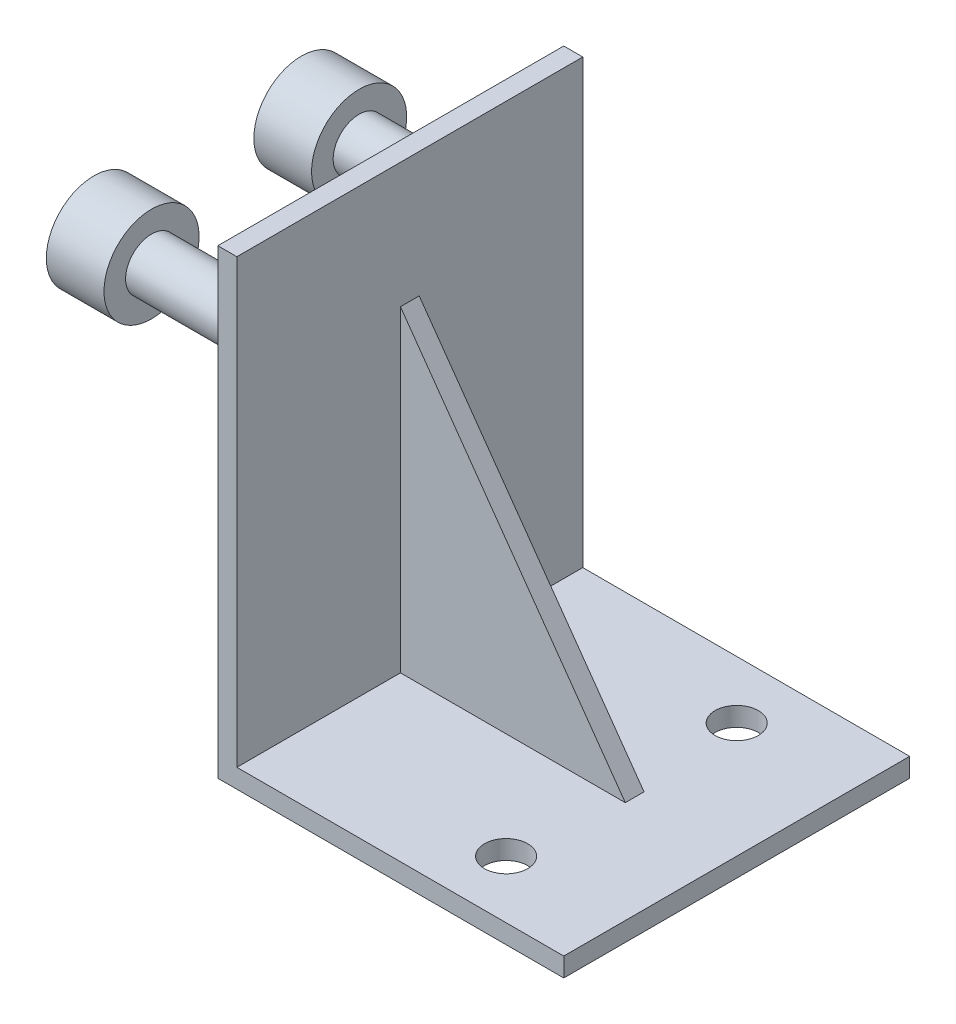
SolidWorks part; units mm, degrees
ref_plane "Front Plane" through (0, 0, 0) normal (0, 0, 1) x (1, 0, 0)
ref_plane "Top Plane" through (0, 0, 0) normal (0, 1, 0) x (1, 0, 0)
ref_plane "Right Plane" through (0, 0, 0) normal (1, 0, 0) x (0, 0, -1)
sketch "Sketch1" plane through (0, 0, 0) normal (0, 0, 1) x (1, 0, 0)
  line L0 (0, 0) -> (30.48, 0)
  line L1 (0, 40.64) -> (1.6764, 40.64)
  line L2 (0, 40.64) -> (0, 0)
  line L4 (1.6764, 40.64) -> (1.6764, 1.6764)
  line L7 (1.6764, 1.6764) -> (30.48, 1.6764)
  line L8 (30.48, 0) -> (30.48, 1.6764)
  dimension "D1" = 1.6764
  dimension "D2" = 30.48
  dimension "D3" = 40.64
extrude "Boss-Extrude1" add sketch "Sketch1" along normal mid plane 30.48 contours L4 L7 L8 L0 L2 L1
sketch "Sketch2" plane through (0, 0, 0) normal (0, 0, 1) x (1, 0, 0)
  line L0 (1.6764, 29.6164) -> (21.4884, 1.6764)
  line L1 (1.6764, 40.64) -> (1.6764, 1.6764) construction
  line L2 (1.6764, 1.6764) -> (30.48, 1.6764) construction
  line L3 (21.4884, 1.6764) -> (1.6764, 1.6764)
  line L4 (1.6764, 1.6764) -> (1.6764, 29.6164)
  dimension "D1" = 27.94
  dimension "D2" = 19.812
extrude "Boss-Extrude2" add sketch "Sketch2" along normal mid plane 1.651
sketch "Sketch3" plane through (0, 1.6764, 0) normal (0, 1, 0) x (1, 0, 0)
  line L0 (30.48, -15.24) -> (30.48, 15.24) construction
  line L1 (1.6764, 15.24) -> (30.48, 15.24) construction
  line L2 (1.6764, -15.24) -> (30.48, -15.24) construction
  circle A0 centre (20.32, 10.16) radius 1.905
  circle A1 centre (20.32, -10.16) radius 1.905
  dimension "D4" = 3.81
  dimension "D1" = 10.16
  dimension "D2" = 5.08
  dimension "D3" = 5.08
extrude "Cut-Extrude1" cut sketch "Sketch3" against normal through all
sketch "Sketch5" plane through (0, 0, 0) normal (-1, 0, 0) x (0, 0, 1)
  line L0 (15.24, 40.64) -> (-15.24, 40.64) construction
  line L1 (15.24, 40.64) -> (15.24, 0) construction
  line L2 (-15.24, 40.64) -> (-15.24, 0) construction
  circle A0 centre (-9.144, 30.226) radius 2.286
  circle A1 centre (9.144, 30.226) radius 2.286
  point P4 (11.43, 30.226)
  point P5 (9.144, 27.94)
  point P6 (-11.43, 30.226)
  dimension "D4" = 4.572
  dimension "D1" = 12.7
  dimension "D2" = 3.81
  dimension "D3" = 3.81
extrude "Boss-Extrude3" add sketch "Sketch5" along normal blind 11.938 contours A0 | A1
sketch "Sketch6" plane through (-11.938, 0, 0) normal (-1, 0, 0) x (0, 0, 1)
  circle A0 centre (-9.144, 30.226) radius 4.191
  circle A1 centre (9.144, 30.226) radius 4.191
  dimension "D1" = 8.382
extrude "Boss-Extrude4" add sketch "Sketch6" along normal blind 5.08
